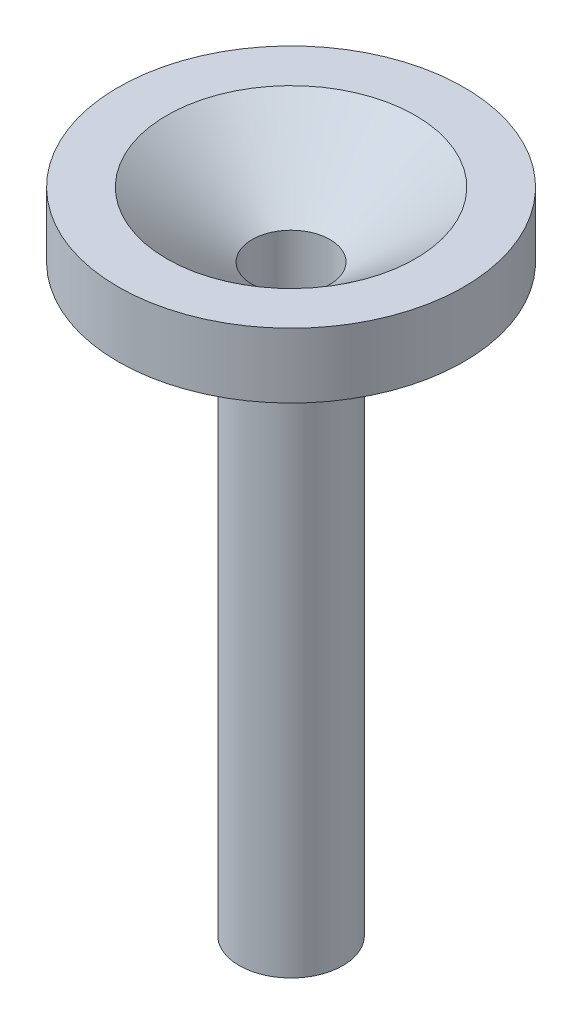
SolidWorks part; units mm, degrees
ref_plane "Front Plane" through (0, 0, 0) normal (0, 0, 1) x (1, 0, 0)
ref_plane "Top Plane" through (0, 0, 0) normal (0, 1, 0) x (1, 0, 0)
ref_plane "Right Plane" through (0, 0, 0) normal (1, 0, 0) x (0, 0, -1)
sketch "Sketch1" plane through (0, 0, 0) normal (0, 0, 1) x (1, 0, 0)
  line L0 (9, -113.7308) -> (9, 16.2692)
  line L1 (9, 16.2692) -> (28.75, 31.2692)
  line L2 (28.75, 31.2692) -> (40, 31.2692)
  line L3 (40, 31.2692) -> (40, 16.2692)
  line L4 (40, 16.2692) -> (12, 16.2692)
  line L5 (12, 16.2692) -> (12, -118.7308)
  line L6 (12, -118.7308) -> (10.5, -118.7308)
  line L7 (10.5, -118.7308) -> (10.5, -113.7308)
  line L8 (10.5, -113.7308) -> (9, -113.7308)
  line L9 (0, 35.0813) -> (0, -29.2862) construction
  dimension "D1" = 9
  dimension "D2" = 12
  dimension "D3" = 10.5
  dimension "D4" = 15
  dimension "D5" = 28.75
  dimension "D6" = 40
  dimension "D7" = 135
  dimension "D8" = 5
revolve "Revolve1" add sketch "Sketch1" angle 360 about L9
